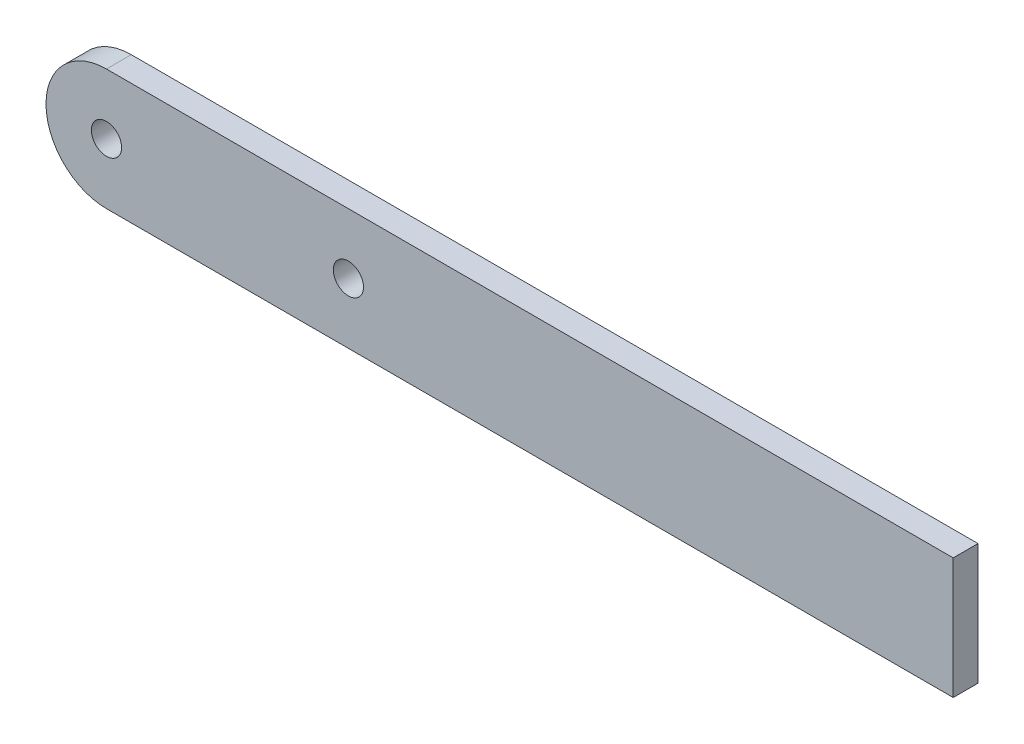
SolidWorks part; units mm, degrees
ref_plane "Front" through (0, 0, 0) normal (0, 0, 1) x (1, 0, 0)
ref_plane "Top" through (0, 0, 0) normal (0, 1, 0) x (1, 0, 0)
ref_plane "Right" through (0, 0, 0) normal (1, 0, 0) x (0, 0, -1)
sketch "Sketch2" plane through (0, 0, 0) normal (0, 0, 1) x (1, 0, 0)
  line L1 (0, 0) -> (177.8, 0)
  line L2 (0, 0) -> (0, 25.4)
  line L3 (0, 25.4) -> (177.8, 25.4)
  line L4 (177.8, 0) -> (177.8, 25.4)
  circle A0 centre (0, 12.7) radius 12.7
  circle A1 centre (50.8, 12.7) radius 12.7
  circle A2 centre (0, 12.7) radius 3.175
  circle A3 centre (50.8, 12.7) radius 3.175
  dimension "D3" = 50.8
  dimension "D4" = 6.35
  dimension "D1" = 177.8
  dimension "D2" = 25.4
extrude "Boss-Extrude2" add sketch "Sketch2" along normal blind 5.207 contours A1 L3 A0 L1 | L2 A0 | L2 A0 | A1 | A1 L1 L4 L3
